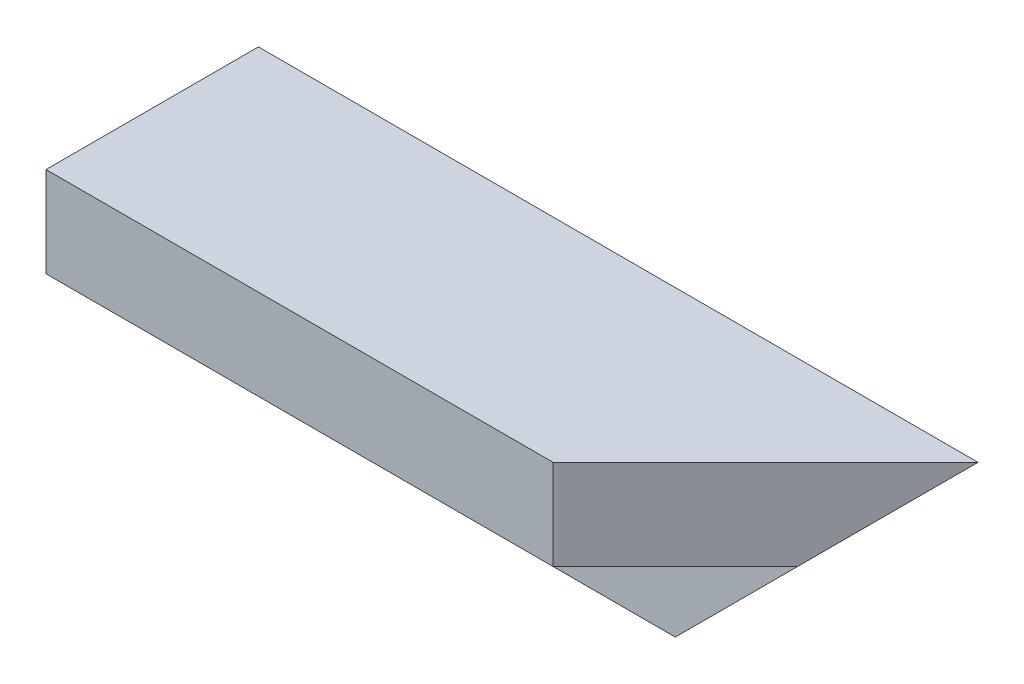
SolidWorks part; units mm, degrees
ref_plane "Plan de face" through (0, 0, 0) normal (0, 0, 1) x (1, 0, 0)
ref_plane "Plan de dessus" through (0, 0, 0) normal (0, 1, 0) x (1, 0, 0)
ref_plane "Plan de droite" through (0, 0, 0) normal (1, 0, 0) x (0, 0, -1)
sketch "Esquisse1" plane through (0, 0, 0) normal (1, 0, 0) x (0, 0, -1)
  line L0 (0, 0) -> (-40, 0)
  line L1 (-40, 0) -> (-40, -17)
  line L2 (-40, -17) -> (-17, -17)
  line L3 (-17, -17) -> (-17, -40)
  line L4 (-17, -40) -> (0, -40)
  line L5 (0, -40) -> (0, 0)
  dimension "D1" = 40
  dimension "D2" = 17
extrude "Boss.-Extru.1" add sketch "Esquisse1" along normal up to vertex (219 mm away) from vertex at 83.5
sketch "Esquisse2" plane through (0, 0, 0) normal (0, 1, 0) x (1, 0, 0)
  line L0 (219, 0) -> (179, -40)
  line L1 (219, -40) -> (83.5, -40) construction
  line L2 (179, -40) -> (219, -40)
  line L3 (219, -40) -> (219, 0)
extrude "Enlèv. mat.-Extru.1" cut sketch "Esquisse2" against normal through all
sketch "Esquisse3" plane through (0, 0, 0) normal (0, 0, -1) x (-1, 0, 0)
  line L0 (-219, 0) -> (-179, -40)
  line L1 (-219, -40) -> (-83.5, -40) construction
  line L2 (-179, -40) -> (-219, -40)
  line L3 (-219, -40) -> (-219, 0)
extrude "Enlèv. mat.-Extru.2" cut sketch "Esquisse3" against normal through all
